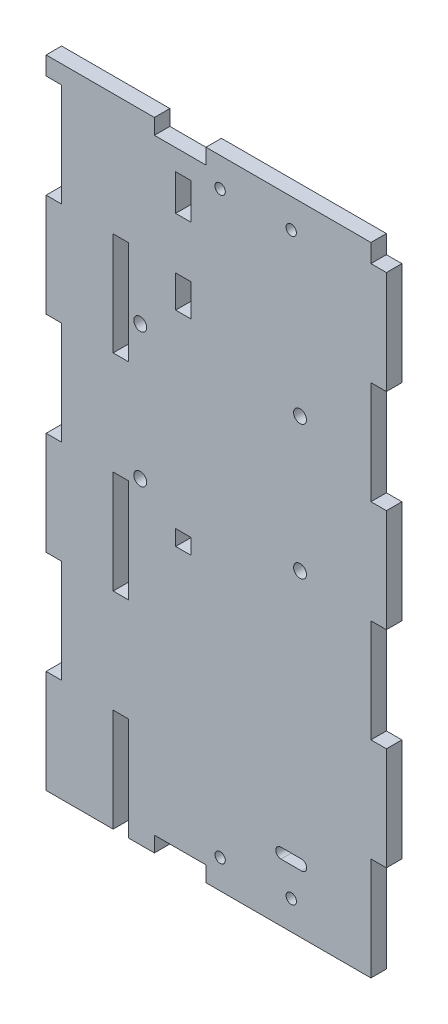
SolidWorks part; units mm, degrees
ref_plane "Face" through (0, 0, 0) normal (0, 0, 1) x (1, 0, 0)
ref_plane "Dessus" through (0, 0, 0) normal (0, 1, 0) x (1, 0, 0)
ref_plane "Droite" through (0, 0, 0) normal (1, 0, 0) x (0, 0, -1)
sketch "Esquisse1" plane through (0, 0, 0) normal (0, 0, 1) x (1, 0, 0)
  line L0 (-395.5689, 174.308) -> (-401.5689, 174.308)
  line L1 (-527.5689, 174.308) -> (-521.5689, 174.308) construction
  line L2 (-521.5689, 174.308) -> (-521.5689, 134.3092) construction
  line L3 (-521.5689, 134.3092) -> (-527.5689, 134.3092) construction
  line L4 (-401.5689, 134.3092) -> (-395.5689, 134.3092)
  line L5 (-527.5689, 94.3074) -> (-521.5689, 94.3074) construction
  line L6 (-521.5689, 94.3074) -> (-521.5689, 54.3086) construction
  line L7 (-521.5689, 54.3086) -> (-527.5689, 54.3086) construction
  line L8 (-395.5689, 94.3074) -> (-401.5689, 94.3074)
  line L9 (-527.5689, 14.3068) -> (-521.5689, 14.3068) construction
  line L10 (-521.5689, 14.3068) -> (-521.5689, -25.692) construction
  line L13 (-527.5689, 174.308) -> (-521.5689, 174.308)
  line L14 (-521.5689, 174.308) -> (-521.5689, 134.3092)
  line L15 (-521.5689, 134.3092) -> (-527.5689, 134.3092)
  line L17 (-527.5689, 94.3074) -> (-521.5689, 94.3074)
  line L18 (-521.5689, 94.3074) -> (-521.5689, 54.3086)
  line L19 (-405.5689, -65.6932) -> (-497.5689, -65.6932) construction
  line L20 (-401.5689, -65.6932) -> (-465.5689, -65.6932)
  line L21 (-395.5689, -25.692) -> (-395.5689, 14.3068)
  line L22 (-401.5689, 181.4099) -> (-465.5689, 181.4099)
  line L24 (-395.5689, 171.4099) -> (-395.5689, -55.6932) construction
  line L25 (-401.5689, 54.3086) -> (-395.5689, 54.3086)
  line L26 (-405.5689, 181.4099) -> (-497.5689, 181.4099) construction
  line L27 (-428.4863, -39.1932) -> (-436.4863, -39.1932) construction
  line L28 (-436.4863, -43.1932) -> (-428.4863, -43.1932) construction
  line L29 (-428.4863, -39.1932) -> (-436.4863, -39.1932)
  line L30 (-436.4863, -43.1932) -> (-428.4863, -43.1932)
  line L31 (-501.5689, -25.6932) -> (-501.5689, -65.6932) construction
  line L32 (-521.5689, 54.3086) -> (-527.5689, 54.3086)
  line L33 (-495.5689, -65.6932) -> (-495.5689, -25.6932) construction
  line L34 (-495.5689, -25.6932) -> (-501.5689, -25.6932) construction
  line L35 (-501.5689, 54.3068) -> (-501.5689, 14.3068) construction
  line L36 (-501.5689, 14.3068) -> (-495.5689, 14.3068) construction
  line L37 (-495.5689, 14.3068) -> (-495.5689, 54.3068) construction
  line L38 (-495.5689, 54.3068) -> (-501.5689, 54.3068) construction
  line L39 (-501.5689, 134.3068) -> (-501.5689, 94.3068) construction
  line L40 (-501.5689, 94.3068) -> (-495.5689, 94.3068) construction
  line L41 (-495.5689, 94.3068) -> (-495.5689, 134.3068) construction
  line L42 (-495.5689, 134.3068) -> (-501.5689, 134.3068) construction
  line L44 (-195.5689, -59.6932) -> (-495.5689, -59.6932) construction
  line L45 (-461.5689, 57.8584) -> (-559.1254, 57.8584) construction
  line L47 (-501.5689, -25.6932) -> (-501.5689, -65.6932)
  line L49 (-495.5689, -65.6932) -> (-495.5689, -25.6932)
  line L50 (-495.5689, -25.6932) -> (-501.5689, -25.6932)
  line L51 (-501.5689, 54.3068) -> (-501.5689, 14.3068)
  line L52 (-501.5689, 14.3068) -> (-495.5689, 14.3068)
  line L53 (-495.5689, 14.3068) -> (-495.5689, 54.3068)
  line L54 (-495.5689, 54.3068) -> (-501.5689, 54.3068)
  line L55 (-501.5689, 134.3068) -> (-501.5689, 94.3068)
  line L56 (-501.5689, 94.3068) -> (-495.5689, 94.3068)
  line L57 (-495.5689, 94.3068) -> (-495.5689, 134.3068)
  line L58 (-495.5689, 134.3068) -> (-501.5689, 134.3068)
  line L63 (-501.5689, -65.6932) -> (-527.5689, -65.6932)
  line L64 (-501.5689, 181.4099) -> (-527.5689, 181.4099)
  line L65 (-471.3189, 167.3068) -> (-471.3189, 153.3068) construction
  line L66 (-471.3189, 153.3068) -> (-477.3189, 153.3068) construction
  line L67 (-477.3189, 153.3068) -> (-477.3189, 167.3068) construction
  line L68 (-477.3189, 167.3068) -> (-471.3189, 167.3068) construction
  line L69 (-471.3189, 133.3068) -> (-471.3189, 120.8068) construction
  line L70 (-395.5689, 14.3068) -> (-401.5689, 14.3068)
  line L71 (-477.3189, 120.8068) -> (-477.3189, 133.3068) construction
  line L72 (-477.3189, 133.3068) -> (-471.3189, 133.3068) construction
  line L80 (-401.5689, -25.692) -> (-395.5689, -25.692)
  line L81 (-471.3189, 167.3068) -> (-471.3189, 153.3068)
  line L82 (-471.3189, 153.3068) -> (-477.3189, 153.3068)
  line L83 (-477.3189, 153.3068) -> (-477.3189, 167.3068)
  line L84 (-477.3189, 167.3068) -> (-471.3189, 167.3068)
  line L85 (-471.3189, 133.3068) -> (-471.3189, 120.8068)
  line L86 (-471.3189, 120.8068) -> (-477.3189, 120.8068)
  line L87 (-477.3189, 120.8068) -> (-477.3189, 133.3068)
  line L88 (-477.3189, 133.3068) -> (-471.3189, 133.3068)
  line L97 (-527.5689, 14.3068) -> (-521.5689, 14.3068)
  line L98 (-521.5689, 14.3068) -> (-521.5689, -25.692)
  line L99 (-521.5689, -25.692) -> (-527.5689, -25.692)
  line L100 (-527.5689, 174.308) -> (-527.5689, 181.4099)
  line L101 (-527.5689, 14.3068) -> (-527.5689, 54.3086)
  line L102 (-527.5689, -65.6932) -> (-527.5689, -25.692)
  line L103 (-527.5689, 94.3074) -> (-527.5689, 134.3092)
  line L104 (-521.5689, -25.692) -> (-527.5689, -25.692) construction
  line L105 (-527.5689, -65.6938) -> (-527.5689, 181.4099) construction
  line L107 (-471.3189, 120.8068) -> (-477.3189, 120.8068) construction
  line L108 (-461.5689, 181.4099) -> (-461.5689, -65.6932) construction
  line L109 (-401.5689, -25.692) -> (-401.5689, -65.6932)
  line L110 (-401.5689, 14.3068) -> (-401.5689, 54.3086)
  line L111 (-401.5689, 94.3074) -> (-401.5689, 134.3092)
  line L112 (-401.5689, 174.308) -> (-401.5689, 181.4099)
  line L113 (-395.5689, 134.3092) -> (-395.5689, 174.308)
  line L114 (-395.5689, 54.3086) -> (-395.5689, 94.3074)
  line L115 (-465.5689, -61.6932) -> (-465.5689, -65.6932) construction
  line L116 (-465.5689, 175.4099) -> (-465.5689, 181.4099)
  line L117 (-485.5689, -61.6932) -> (-485.5689, -65.6932) construction
  line L118 (-485.5689, 175.4099) -> (-465.5689, 175.4099)
  line L119 (-465.5689, -59.6932) -> (-465.5689, -65.6932)
  line L121 (-485.5689, -59.6932) -> (-485.5689, -65.6932)
  line L122 (-485.5689, -59.6932) -> (-465.5689, -59.6932)
  line L123 (-485.5689, -65.6932) -> (-495.5689, -65.6932)
  line L124 (-485.5689, 175.4099) -> (-485.5689, 181.4099)
  line L125 (-485.5689, 181.4099) -> (-501.5689, 181.4099)
  line L130 (-471.3189, 41.4099) -> (-471.3189, 47.4099)
  line L131 (-477.3189, 41.4099) -> (-471.3189, 41.4099)
  line L132 (-477.3189, 47.4099) -> (-477.3189, 41.4099)
  line L133 (-471.3189, 47.4099) -> (-477.3189, 47.4099)
  line L134 (-471.3189, 41.4099) -> (-471.3189, 47.4099)
  line L136 (-477.3189, 47.4099) -> (-477.3189, 41.4099)
  line L137 (-471.3189, 47.4099) -> (-477.3189, 47.4099)
  line L139 (-477.3189, 41.4099) -> (-471.3189, 41.4099)
  circle A0 centre (-495.0689, 57.3068) radius 2.5 construction
  circle A1 centre (-495.0689, 109.3068) radius 2.5 construction
  circle A2 centre (-433.0689, 109.3068) radius 2.5 construction
  circle A4 centre (-433.0689, 57.3068) radius 2.5 construction
  circle A5 centre (-495.0689, 57.3068) radius 2.5 construction
  circle A6 centre (-495.0689, 109.3068) radius 2.5 construction
  circle A7 centre (-433.0689, 109.3068) radius 2.5 construction
  circle A9 centre (-433.0689, 57.3068) radius 2.5 construction
  circle A10 centre (-491.0689, 57.3068) radius 2.5
  circle A11 centre (-491.0689, 109.3068) radius 2.5
  circle A12 centre (-429.0689, 109.3068) radius 2.5
  circle A13 centre (-429.0689, 57.3068) radius 2.5
  circle A17 centre (-460.0689, 170.1599) radius 2 construction
  circle A18 centre (-432.4863, 170.1599) radius 2 construction
  circle A21 centre (-460.0689, -54.4432) radius 2 construction
  circle A22 centre (-432.4863, -54.4432) radius 2 construction
  arc A23 (-428.4863, -43.1932) -> (-428.4863, -39.1932) centre (-428.4863, -41.1932) ccw construction
  arc A24 (-436.4863, -39.1932) -> (-436.4863, -43.1932) centre (-436.4863, -41.1932) ccw construction
  circle A29 centre (-460.0689, 170.1599) radius 2
  circle A30 centre (-432.4863, 170.1599) radius 2
  circle A33 centre (-460.0689, -54.4432) radius 2
  circle A34 centre (-432.4863, -54.4432) radius 2
  arc A35 (-428.4863, -43.1932) -> (-428.4863, -39.1932) centre (-428.4863, -41.1932) ccw
  arc A36 (-436.4863, -39.1932) -> (-436.4863, -43.1932) centre (-436.4863, -41.1932) ccw
  dimension "D1" = 2
  dimension "D2" = 4
  dimension "D3" = 0
extrude "Boss.-Extru.1" add sketch "Esquisse1" against normal blind 6
